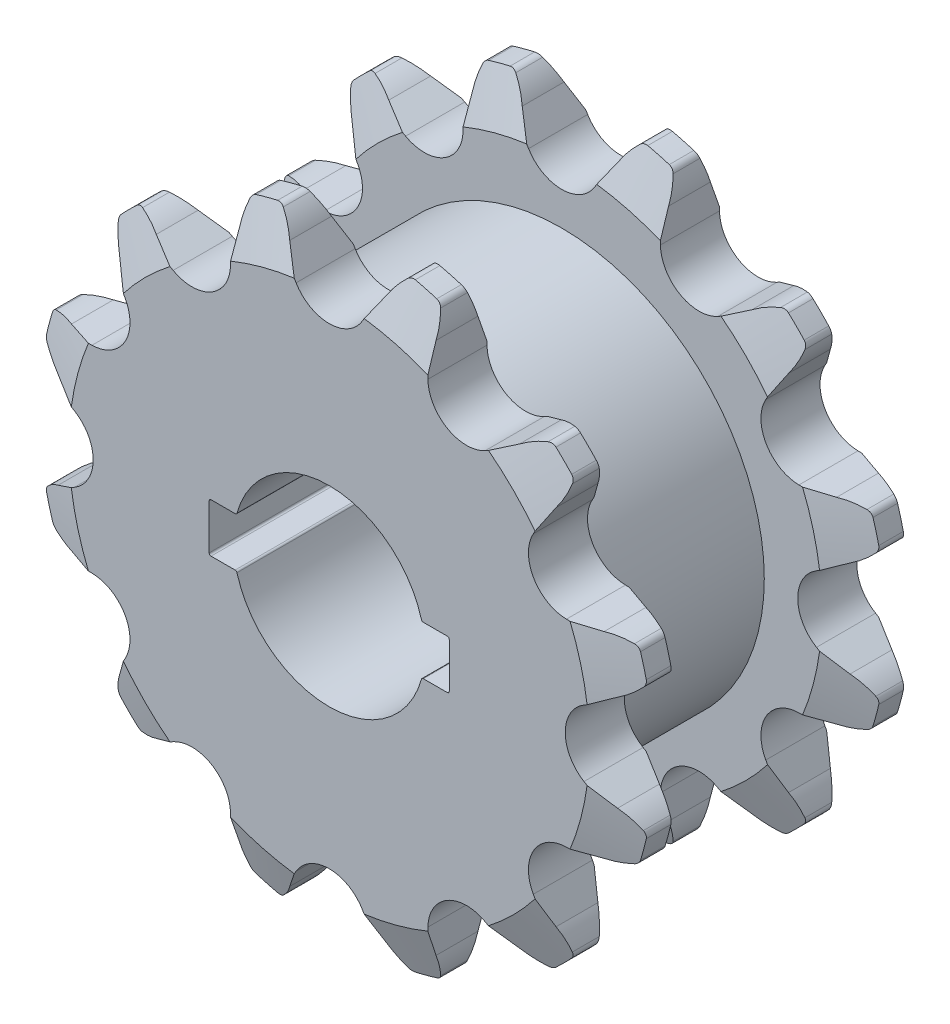
SolidWorks part; units mm, degrees
material "6061-T6 (SS)"
ref_plane "Front Plane" through (0, 0, 0) normal (0, 0, 1) x (1, 0, 0)
ref_plane "Top Plane" through (0, 0, 0) normal (0, 1, 0) x (1, 0, 0)
ref_plane "Right Plane" through (0, 0, 0) normal (1, 0, 0) x (0, 0, -1)
ref_plane "Plane1" through (0, 0, 5.8166) normal (0, 0, 1) x (1, 0, 0)
sketch "Sketch1" plane through (0, 0, 5.8166) normal (0, 0, 1) x (1, 0, 0)
  line L0 (0, 76.6001) -> (0, -76.6001) construction
  line L1 (-124.3299, 0) -> (133.2713, 0) construction
  line L2 (6.2139, 1.6383) -> (8.0518, 1.6383)
  line L3 (8.0518, 1.6383) -> (8.0518, -1.6383)
  line L4 (8.0518, -1.6383) -> (6.2139, -1.6383)
  line L5 (-6.2139, 1.6383) -> (-8.0518, 1.6383)
  line L6 (-8.0518, 1.6383) -> (-8.0518, -1.6383)
  line L7 (-8.0518, -1.6383) -> (-6.2139, -1.6383)
  arc A0 (-6.2139, -1.6383) -> (6.2139, -1.6383) centre (0, 0) ccw
  circle A1 centre (0, 0) radius 20.6324
  arc A2 (6.2139, 1.6383) -> (-6.2139, 1.6383) centre (0, 0) ccw
  dimension "D1" = 12.8524
  dimension "D2" = 41.2648
  dimension "D3" = 3.2766
  dimension "D4" = 3.2766
  dimension "D5" = 16.1036
extrude "Extrude1" add sketch "Sketch1" along normal blind 3.9624
sketch "Sketch2" plane through (0, 0, 5.8166) normal (0, 0, -1) x (-1, 0, 0)
  line L6 (8.0518, 1.6383) -> (6.2139, 1.6383)
  line L7 (8.0518, -1.6383) -> (8.0518, 1.6383)
  line L8 (6.2139, -1.6383) -> (8.0518, -1.6383)
  line L9 (-8.0518, -1.6383) -> (-6.2139, -1.6383)
  line L10 (-8.0518, 1.6383) -> (-8.0518, -1.6383)
  line L11 (-6.2139, 1.6383) -> (-8.0518, 1.6383)
  line L12 (8.0518, 1.6383) -> (6.2139, 1.6383)
  line L13 (8.0518, -1.6383) -> (8.0518, 1.6383)
  line L14 (6.2139, -1.6383) -> (8.0518, -1.6383)
  line L15 (-8.0518, -1.6383) -> (-6.2139, -1.6383)
  line L16 (-8.0518, 1.6383) -> (-8.0518, -1.6383)
  line L17 (-6.2139, 1.6383) -> (-8.0518, 1.6383)
  circle A0 centre (0, 0) radius 13.589
  arc A3 (6.2139, 1.6383) -> (-6.2139, 1.6383) centre (0, 0) ccw
  arc A4 (-6.2139, -1.6383) -> (6.2139, -1.6383) centre (0, 0) ccw
  arc A5 (6.2139, 1.6383) -> (-6.2139, 1.6383) centre (0, 0) ccw
  arc A6 (-6.2139, -1.6383) -> (6.2139, -1.6383) centre (0, 0) ccw
  dimension "D1" = 27.178
  dimension "D2" = 0
extrude "Extrude2" add sketch "Sketch2" along normal blind 11.6332
mirror "Mirror5" about plane through (0, 0, 0) normal (0, 0, 1) of "Extrude1"
sketch "Sketch3" plane through (0, 0, 9.779) normal (0, 0, 1) x (1, 0, 0)
  line L0 (0, 20.6324) -> (0, -20.6324) construction
  line L1 (-20.6324, 0) -> (20.6324, 0) construction
  line L2 (2.2225, 17.0912) -> (2.6028, 17.7259)
  line L3 (-2.6028, 17.7259) -> (-2.2225, 17.0912)
  line L4 (-2.6028, 17.7259) -> (-3.2258, 18.7659)
  line L5 (3.2258, 18.7659) -> (2.6028, 17.7259)
  circle A0 centre (0, 0) radius 20.6324 construction
  arc A1 (-20.6324, 0) -> (20.6324, 0) centre (0, 0) ccw
  arc A2 (-2.2225, 17.0912) -> (2.2225, 17.0912) centre (0, 18.4226) ccw
  arc A3 (-3.2258, 18.7659) -> (-4.3664, 20.1651) centre (-7.069, 16.7975) ccw
  arc A4 (4.3664, 20.1651) -> (3.2258, 18.7659) centre (7.069, 16.7975) ccw
  arc A5 (4.3664, 20.1651) -> (-4.3664, 20.1651) centre (0, 0) ccw
  point P10 (0, 15.8318)
  circle M8 centre (0, 0) radius 20.6324
  dimension "D1" = 2.5908
  dimension "D4" = 4.318
  dimension "D6" = 6.4516
  dimension "D2" = 4.8006
  dimension "D3" = 8.7327
  dimension "D5" = 5.2055
  dimension "D7" = 2.9341
  dimension "D8" = 1.8941
  dimension "D9" = 4.445
extrude "Extrude3" cut sketch "Sketch3" against normal up to surface (19.558 mm away) contours A4 A3 L4 L3 A2 L2 L5 M8
chamfer "Chamfer1" distance 1.1582 distance2 3.175 2 edges at (0, -20.6324, 9.779) (0, -20.6324, -5.8166)
chamfer "Chamfer2" distance 3.175 distance2 1.1582 2 edges at (0, -20.6324, 5.8166) (0, -20.6324, -9.779)
pattern_circular "CirPattern1" count 12 over 360 about axis through (0, 0, 0) along (0, 0, 1) of "Extrude3"
fillet "Fillet1" radius 0.127 8 edges at (8.0518, -1.6383, 0) (8.0518, 1.6383, 0) (-8.0518, 1.6383, 0) (-8.0518, -1.6383, 0) (6.2139, 1.6383, 0) (6.2139, -1.6383, 0) (-6.2139, -1.6383, 0) (-6.2139, 1.6383, 0)
fillet "Fillet2" radius 0.508 48 edges at (-13.8639, -15.2803, -7.7978) (-15.2803, -13.8639, -7.7978) (-6.3012, -19.6467, 7.7978) (-4.3664, -20.1651, 7.7978) (-6.3012, -19.6467, -7.7978) (-4.3664, -20.1651, -7.7978) (4.3664, -20.1651, -7.7978) (6.3012, -19.6467, -7.7978) (4.3664, -20.1651, 7.7978) (6.3012, -19.6467, 7.7978) (13.8639, -15.2803, -7.7978) (15.2803, -13.8639, -7.7978) (13.8639, -15.2803, 7.7978) (15.2803, -13.8639, 7.7978) (19.6467, -6.3012, 7.7978) (20.1651, -4.3664, 7.7978) (19.6467, -6.3012, -7.7978) (20.1651, -4.3664, -7.7978) (20.1651, 4.3664, -7.7978) (19.6467, 6.3012, -7.7978) (15.2803, 13.8639, -7.7978) (13.8639, 15.2803, -7.7978) (20.1651, 4.3664, 7.7978) (19.6467, 6.3012, 7.7978) (15.2803, 13.8639, 7.7978) (13.8639, 15.2803, 7.7978) (6.3012, 19.6467, -7.7978) (4.3664, 20.1651, -7.7978) (-4.3664, 20.1651, -7.7978) (-6.3012, 19.6467, -7.7978) (6.3012, 19.6467, 7.7978) (4.3664, 20.1651, 7.7978) (-4.3664, 20.1651, 7.7978) (-6.3012, 19.6467, 7.7978) (-15.2803, 13.8639, 7.7978) (-13.8639, 15.2803, 7.7978) (-13.8639, 15.2803, -7.7978) (-15.2803, 13.8639, -7.7978) (-19.6467, 6.3012, -7.7978) (-20.1651, 4.3664, -7.7978) (-19.6467, -6.3012, -7.7978) (-20.1651, -4.3664, -7.7978) (-13.8639, -15.2803, 7.7978) (-15.2803, -13.8639, 7.7978) (-19.6467, -6.3012, 7.7978) (-20.1651, -4.3664, 7.7978) (-20.1651, 4.3664, 7.7978) (-19.6467, 6.3012, 7.7978)
ref_plane "Plane2" through (0, 0, 7.7978) normal (0, 0, 1) x (1, 0, 0)
ref_plane "Plane3" through (0, 0, -7.7978) normal (0, 0, -1) x (-1, 0, 0)
sketch "Sketch4" plane through (0, 0, 7.7978) normal (0, 0, 1) x (1, 0, 0)
  circle A0 centre (0, 0) radius 17.4574
  circle A1 centre (0, 0) radius 17.4574 construction
sketch "Sketch5" plane through (0, 0, -7.7978) normal (0, 0, -1) x (-1, 0, 0)
  circle A0 centre (0, 0) radius 17.4574
  circle A2 centre (0, 0) radius 17.4574 construction
